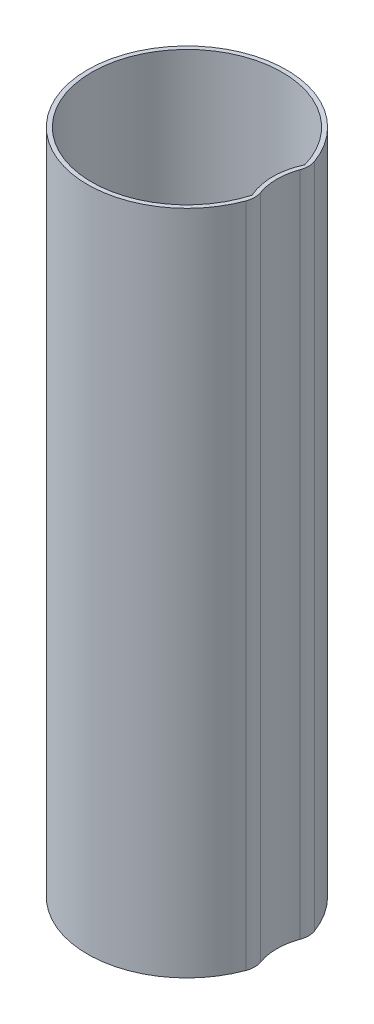
SolidWorks part; units mm, degrees
material "Cardboard"
ref_plane "Frontal Plane" through (0, 0, 0) normal (0, 0, 1) x (1, 0, 0)
ref_plane "Horizontal Plane" through (0, 0, 0) normal (0, 1, 0) x (1, 0, 0)
ref_plane "Profile Plane" through (0, 0, 0) normal (1, 0, 0) x (0, 0, -1)
sketch "Sketch1" plane through (0, 0, 0) normal (0, 1, 0) x (1, 0, 0)
  line L0 (0, 0) -> (11.3319, 0) construction
  line L1 (0, 0) -> (11.9688, 0) construction
  arc A1 (9.0754, 2.4491) -> (9.0754, -2.4491) centre (0, 0) ccw
  circle A2 centre (14, 0) radius 5.9 construction
  circle A3 centre (14, 0) radius 5.5 construction
  arc A4 (8.6496, 2.4867) -> (8.6496, -2.4867) centre (14, 0) ccw
  arc A5 (9.0754, 2.4491) -> (9.0754, -2.4491) centre (14, 0) ccw
  arc A6 (8.6496, 2.4867) -> (8.6496, -2.4867) centre (0, 0) ccw
  dimension "D1" = 18
  dimension "D2" = 18.8
extrude "Boss-Extrude1" add sketch "Sketch1" along normal blind 63
fillet "Fillet2" radius 2 2 edges at (9.0754, 31.5, -2.4491) (9.0754, 31.5, 2.4491)
